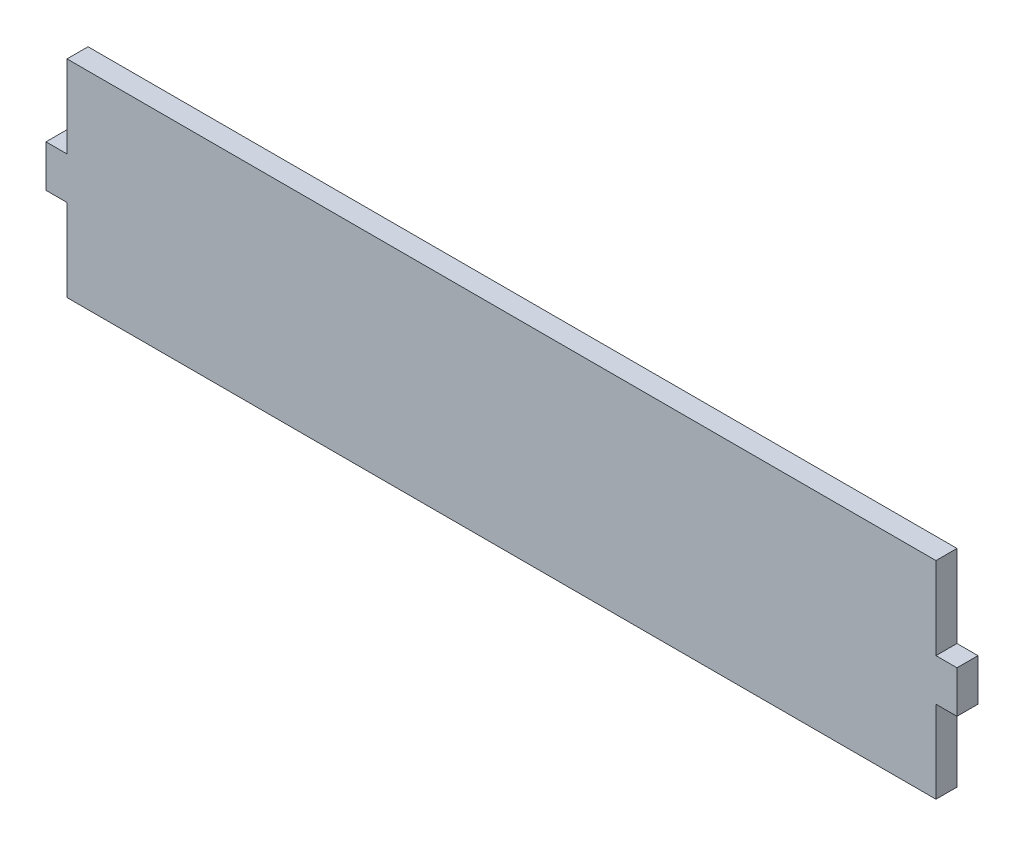
SolidWorks part; units mm, degrees
ref_plane "Front Plane" through (0, 0, 0) normal (0, 0, 1) x (1, 0, 0)
ref_plane "Top Plane" through (0, 0, 0) normal (0, 1, 0) x (1, 0, 0)
ref_plane "Right Plane" through (0, 0, 0) normal (1, 0, 0) x (0, 0, -1)
sketch "Sketch2" plane through (0, 0, 0) normal (0, 1, 0) x (1, 0, 0)
  line L0 (0, 0) -> (0, 6) construction
  dimension "D1" = 6
sketch "Sketch1" plane through (0, 0, 0) normal (0, 0, 1) x (1, 0, 0)
  line L1 (-130, -29.5) -> (130, -29.5)
  line L2 (-130, -29.5) -> (-130, 29.5)
  line L3 (-130, 29.5) -> (130, 29.5)
  line L4 (130, -29.5) -> (130, 29.5)
  line L5 (-130, -29.5) -> (130, 29.5) construction
  line L6 (-130, 29.5) -> (130, -29.5) construction
  line L7 (-130, 29.5) -> (-124, 29.5)
  line L8 (-130, 29.5) -> (-130, 6)
  line L9 (-130, 6) -> (-124, 6)
  line L10 (-124, 29.5) -> (-124, 6)
  line L11 (-124, -29.5) -> (-130, -29.5)
  line L12 (-124, -29.5) -> (-124, -6)
  line L13 (-124, -6) -> (-130, -6)
  line L14 (-130, -29.5) -> (-130, -6)
  line L15 (130, 29.5) -> (124, 29.5)
  line L16 (130, 29.5) -> (130, 6)
  line L17 (130, 6) -> (124, 6)
  line L18 (124, 29.5) -> (124, 6)
  line L19 (130, -29.5) -> (124, -29.5)
  line L20 (130, -29.5) -> (130, -6)
  line L21 (130, -6) -> (124, -6)
  line L22 (124, -29.5) -> (124, -6)
  point P0 (0, 0)
  dimension "D1" = 260
  dimension "D2" = 59
  dimension "D3" = 12
  dimension "D4" = 6
extrude "Boss-Extrude1" add sketch "Sketch1" against normal up to vertex (6 mm away) contours L1 L22 L21 L4 L17 L18 L3 L10 L9 L2 L13 L12 up to point (0, 0, -6)
equation "\"t_wood\"= 6' Thickness of the wood"
equation "\"t_glass\"= 2.5'Thickness of glass panels"
equation "\"w_glass\"= 248"
equation "\"h_glass\"= 167"
equation "\"h_food_internal\" = 60"
equation "\"entry_height\"= 20"
equation "\"entry diameter\"= 8"
equation "\"glass_bottom_overlap\"= 8"
equation "\"default_finger_size\"= 12"
equation "\"brood_depth\"= 42"
equation "\"outer_box_depth\" = \"brood_depth\" + ( 2 * \"t_glass\" ) + ( 2 * \"t_wood\" )"
equation "\"outer_box_width\"= \"w_glass\" + ( 2 * \"t_wood\" )"
equation "\"food_top_clearance\"= 10"
equation "\"outer_box_height\"= \"t_wood\" + \"h_glass\" + \"t_wood\" + \"h_food_internal\" + \"food_top_clearance\" + \"t_wood\""
equation "\"food_internal_depth\"= \"brood_depth\" + \"t_glass\" + \"t_glass\" - \"t_wood\" - \"t_wood\""
equation "\"food_channel_clearance_width\"= 14"
equation "\"bar_top_play\"= 4.5"
equation "\"bar_entry_angle\"= 10"
equation "\"bar_width\"= 20"
equation "\"entry_disk_play\"= 0.3"
equation "\"D1@Sketch2\"=\"t_wood\""
equation "\"D1@Sketch1\"=\"outer_box_width\""
equation "\"D2@Sketch1\"=\"outer_box_depth\""
equation "\"D3@Sketch1\"=\"default_finger_size\""
equation "\"D4@Sketch1\"=\"t_wood\""
